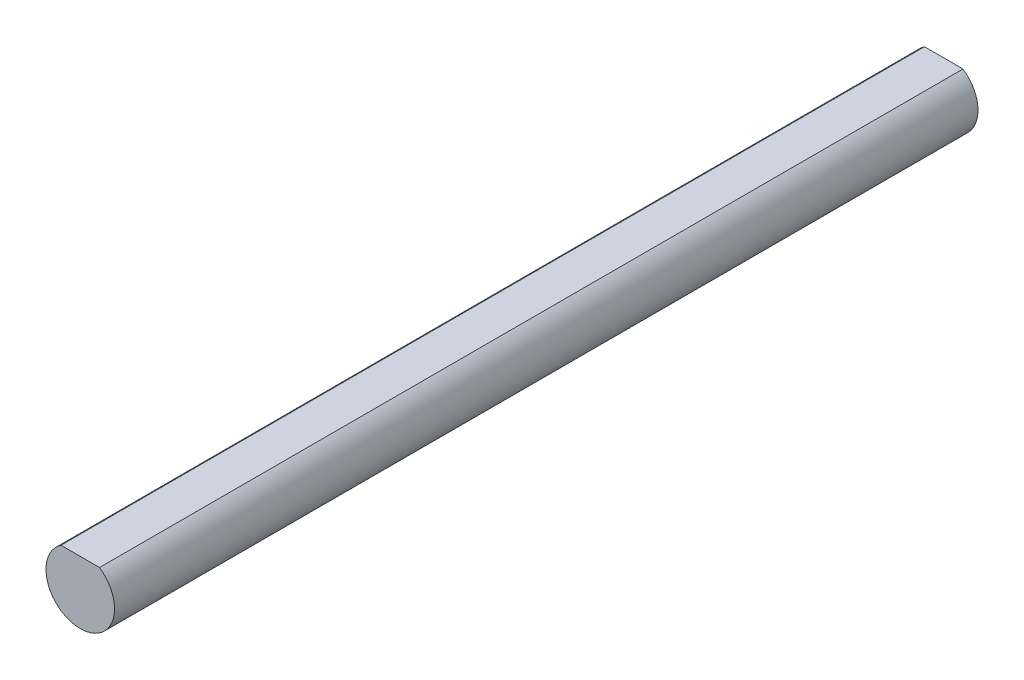
SolidWorks part; units mm, degrees
material "5052-H32"
ref_plane "Front Plane" through (0, 0, 0) normal (0, 0, 1) x (1, 0, 0)
ref_plane "Top Plane" through (0, 0, 0) normal (0, 1, 0) x (1, 0, 0)
ref_plane "Right Plane" through (0, 0, 0) normal (1, 0, 0) x (0, 0, -1)
sketch "Sketch1" plane through (0, 0, 0) normal (0, 0, 1) x (1, 0, 0)
  line L0 (-1.7861, 2.625) -> (1.7861, 2.625)
  arc A0 (-1.7861, 2.625) -> (1.7861, 2.625) centre (0, 0) ccw
  dimension "D1" = 6.35
  dimension "D2" = 2.625
extrude "Boss-Extrude1" add sketch "Sketch1" along normal blind 80
